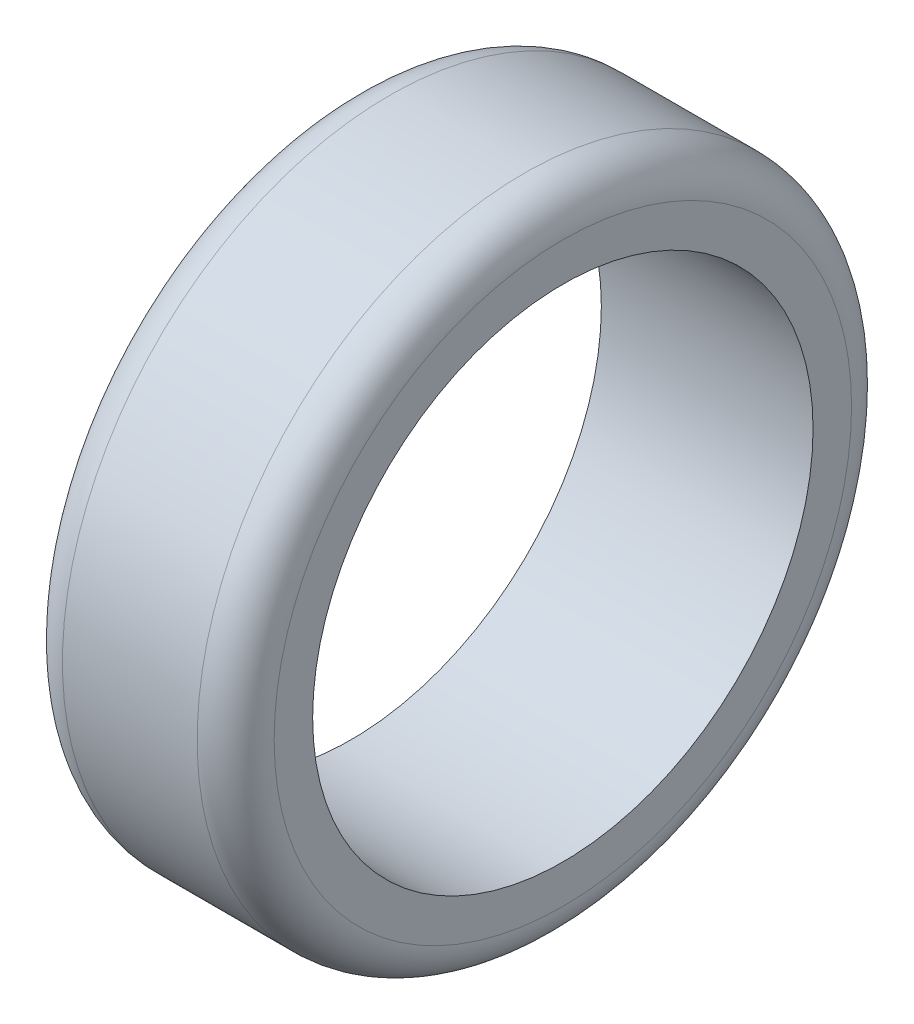
SolidWorks part; units mm, degrees
ref_plane "前视基准面" through (0, 0, 0) normal (0, 0, 1) x (1, 0, 0)
ref_plane "上视基准面" through (0, 0, 0) normal (0, 1, 0) x (1, 0, 0)
ref_plane "右视基准面" through (0, 0, 0) normal (1, 0, 0) x (0, 0, -1)
other "Configuration Table"
sketch "草图1" plane through (0, 0, 0) normal (1, 0, 0) x (0, 0, -1)
  circle A0 centre (0, 0) radius 34
  dimension "D1" = 68
extrude "凸台-拉伸1" add sketch "草图1" along normal blind 22
sketch "草图2" plane through (0, 0, 0) normal (-1, 0, 0) x (0, 0, 1)
  circle A0 centre (0, 0) radius 26
  dimension "D1" = 52
extrude "切除-拉伸1" cut sketch "草图2" against normal blind 22
fillet "圆角1" radius 4 2 edges at (22, 0, -34) (0, 0, -34)
